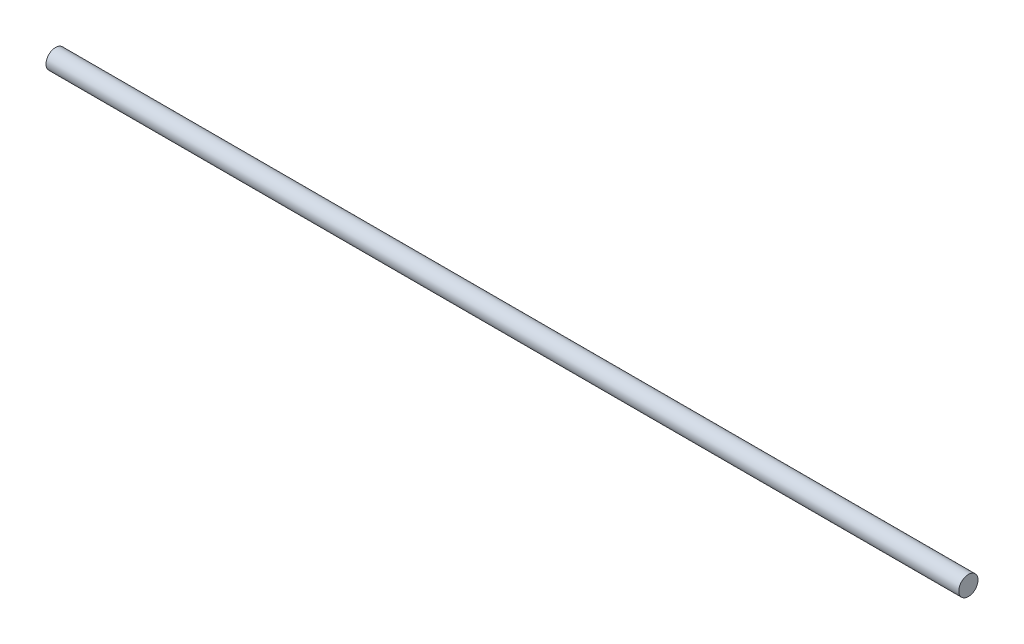
SolidWorks part; units mm, degrees
ref_plane "Alzado" through (0, 0, 0) normal (0, 0, 1) x (1, 0, 0)
ref_plane "Planta" through (0, 0, 0) normal (0, 1, 0) x (1, 0, 0)
ref_plane "Vista lateral" through (0, 0, 0) normal (1, 0, 0) x (0, 0, -1)
sketch3d "Croquis3D1"
  line L0 (0, 0, 0) -> (-1300, 0, 0)
  dimension "D1" = 1300
sketch "Croquis2" plane through (0, 0, 0) normal (1, 0, 0) x (0, 0, -1)
  circle A0 centre (0, 0) radius 13.7
  dimension "D1" = 27.4
sweep "Barrer1" add profiles "Croquis2" path "Croquis3D1"
